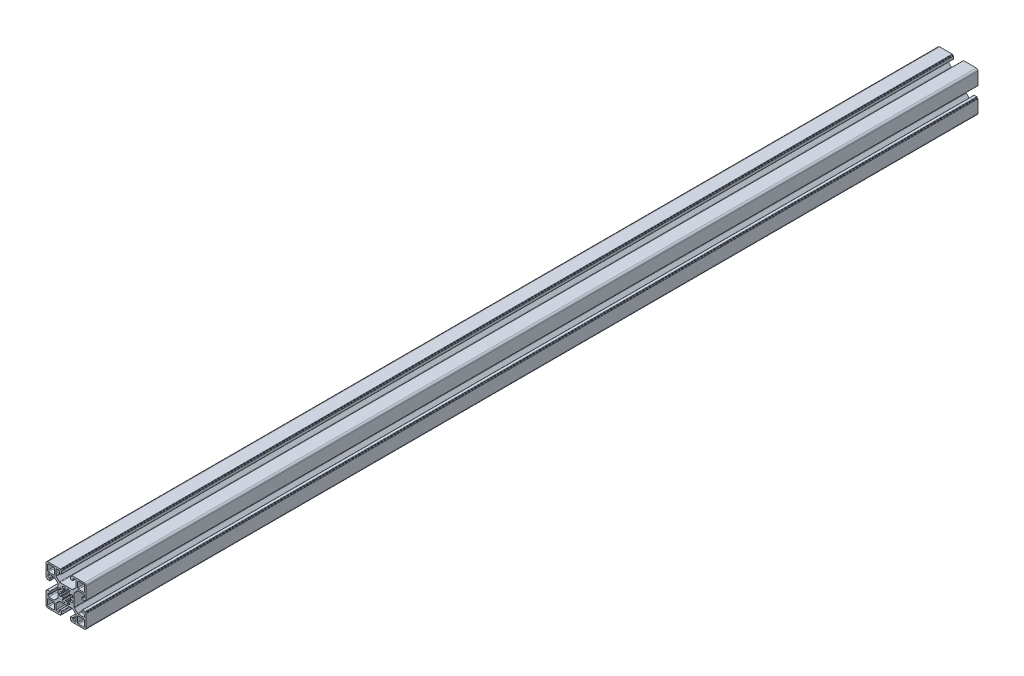
SolidWorks part; units mm, degrees
material "6063 T5"
ref_plane "Спереди" through (0, 0, 0) normal (0, 0, 1) x (1, 0, 0)
ref_plane "Сверху" through (0, 0, 0) normal (0, 1, 0) x (1, 0, 0)
ref_plane "Справа" through (0, 0, 0) normal (1, 0, 0) x (0, 0, -1)
sketch "Эскиз1" plane through (0, 0, 0) normal (0, 0, 1) x (1, 0, 0)
  line L0 (-19.98, 20.5457) -> (20.02, 20.5457) construction
  line L1 (-22.5, 11.25) -> (-22.5, 20.5)
  line L2 (-20.5, 22.5) -> (-11.25, 22.5)
  line L3 (11.25, 22.5) -> (20.5, 22.5)
  line L4 (-14, 13) -> (-19.8, 13)
  line L5 (-13, 14) -> (-13, 19.8)
  line L6 (-14, 20.8) -> (-19.8, 20.8)
  line L7 (-20.8, 14) -> (-20.8, 19.8)
  line L8 (22.5, 20.5) -> (22.5, 11.25)
  line L9 (13, 14) -> (13, 19.8)
  line L10 (14, 13) -> (19.8, 13)
  line L11 (20.8, 14) -> (20.8, 19.8)
  line L12 (14, 20.8) -> (19.8, 20.8)
  line L13 (22.5, -11.25) -> (22.5, -20.5)
  line L14 (20.5, -22.5) -> (11.25, -22.5)
  line L15 (14, -13) -> (19.8, -13)
  line L16 (13, -14) -> (13, -19.8)
  line L17 (14, -20.8) -> (19.8, -20.8)
  line L18 (20.8, -14) -> (20.8, -19.8)
  line L19 (-11.25, -22.5) -> (-20.5, -22.5)
  line L20 (-22.5, -20.5) -> (-22.5, -11.25)
  line L21 (-13, -14) -> (-13, -19.8)
  line L22 (-14, -13) -> (-19.8, -13)
  line L23 (-20.8, -14) -> (-20.8, -19.8)
  line L24 (-14, -20.8) -> (-19.8, -20.8)
  line L25 (0, 0) -> (-13, 14) construction
  line L26 (-22.5383, 27.0237) -> (22.4617, 27.0237) construction
  arc A0 (-22.5, 20.5) -> (-20.5, 22.5) centre (-20.5, 20.5) cw
  arc A1 (-19.8, 20.8) -> (-20.8, 19.8) centre (-19.8, 19.8) ccw
  arc A2 (-19.8, 13) -> (-20.8, 14) centre (-19.8, 14) cw
  arc A3 (-14, 13) -> (-13, 14) centre (-14, 14) ccw
  arc A4 (-13, 19.8) -> (-14, 20.8) centre (-14, 19.8) ccw
  arc A6 (20.5, 22.5) -> (22.5, 20.5) centre (20.5, 20.5) cw
  arc A7 (20.8, 19.8) -> (19.8, 20.8) centre (19.8, 19.8) ccw
  arc A8 (13, 19.8) -> (14, 20.8) centre (14, 19.8) cw
  arc A9 (13, 14) -> (14, 13) centre (14, 14) ccw
  arc A10 (19.8, 13) -> (20.8, 14) centre (19.8, 14) ccw
  arc A11 (22.5, -20.5) -> (20.5, -22.5) centre (20.5, -20.5) cw
  arc A12 (19.8, -20.8) -> (20.8, -19.8) centre (19.8, -19.8) ccw
  arc A13 (19.8, -13) -> (20.8, -14) centre (19.8, -14) cw
  arc A14 (14, -13) -> (13, -14) centre (14, -14) ccw
  arc A15 (13, -19.8) -> (14, -20.8) centre (14, -19.8) ccw
  arc A16 (-20.5, -22.5) -> (-22.5, -20.5) centre (-20.5, -20.5) cw
  arc A17 (-20.8, -19.8) -> (-19.8, -20.8) centre (-19.8, -19.8) ccw
  arc A18 (-13, -19.8) -> (-14, -20.8) centre (-14, -19.8) cw
  arc A19 (-13, -14) -> (-14, -13) centre (-14, -14) ccw
  arc A20 (-19.8, -13) -> (-20.8, -14) centre (-19.8, -14) ccw
  point P5 (0, 0)
  line B0 (-22.5, 11.25) -> (-22.5, 6.4)
  line B1 (-22.2, 6.1) -> (-21.8, 6.1)
  line B2 (-21.5, 5.8) -> (-21.5, 5.4)
  line B3 (-21.2, 5.1) -> (-18.3, 5.1)
  line B4 (-18, 5.4) -> (-18, 7.3)
  line B5 (-18.3, 7.6) -> (-19.5, 7.6)
  line B6 (-20.5, 8.6) -> (-20.5, 10.25)
  line B7 (-19.5, 11.25) -> (-13.5642, 11.25)
  line B8 (-12.8571, 10.9571) -> (-9.4429, 7.5429)
  line B9 (-9.15, 6.8358) -> (-9.15, -6.8358)
  line B10 (-9.15, 0) -> (-22.5, 0) construction
  line B11 (-12.8571, -10.9571) -> (-9.4429, -7.5429)
  line B12 (-19.5, -11.25) -> (-13.5642, -11.25)
  line B13 (-20.5, -8.6) -> (-20.5, -10.25)
  line B14 (-18.3, -7.6) -> (-19.5, -7.6)
  line B15 (-18, -5.4) -> (-18, -7.3)
  line B16 (-21.2, -5.1) -> (-18.3, -5.1)
  line B17 (-21.5, -5.8) -> (-21.5, -5.4)
  line B18 (-22.2, -6.1) -> (-21.8, -6.1)
  line B19 (-22.5, -11.25) -> (-22.5, -6.4)
  arc B20 (-18, 7.3) -> (-18.3, 7.6) centre (-18.3, 7.3) ccw
  arc B21 (-18.3, 5.1) -> (-18, 5.4) centre (-18.3, 5.4) ccw
  arc B22 (-21.5, 5.4) -> (-21.2, 5.1) centre (-21.2, 5.4) ccw
  arc B23 (-21.8, 6.1) -> (-21.5, 5.8) centre (-21.8, 5.8) cw
  arc B24 (-22.5, 6.4) -> (-22.2, 6.1) centre (-22.2, 6.4) ccw
  arc B25 (-9.4429, 7.5429) -> (-9.15, 6.8358) centre (-10.15, 6.8358) cw
  arc B26 (-13.5642, 11.25) -> (-12.8571, 10.9571) centre (-13.5642, 10.25) cw
  arc B27 (-20.5, 10.25) -> (-19.5, 11.25) centre (-19.5, 10.25) cw
  arc B28 (-19.5, 7.6) -> (-20.5, 8.6) centre (-19.5, 8.6) cw
  arc B29 (-19.5, -7.6) -> (-20.5, -8.6) centre (-19.5, -8.6) ccw
  arc B30 (-20.5, -10.25) -> (-19.5, -11.25) centre (-19.5, -10.25) ccw
  arc B31 (-13.5642, -11.25) -> (-12.8571, -10.9571) centre (-13.5642, -10.25) ccw
  arc B32 (-9.4429, -7.5429) -> (-9.15, -6.8358) centre (-10.15, -6.8358) ccw
  arc B33 (-22.5, -6.4) -> (-22.2, -6.1) centre (-22.2, -6.4) cw
  arc B34 (-21.8, -6.1) -> (-21.5, -5.8) centre (-21.8, -5.8) ccw
  arc B35 (-21.5, -5.4) -> (-21.2, -5.1) centre (-21.2, -5.4) cw
  arc B36 (-18.3, -5.1) -> (-18, -5.4) centre (-18.3, -5.4) cw
  arc B37 (-18, -7.3) -> (-18.3, -7.6) centre (-18.3, -7.3) cw
  line B38 (11.25, 22.5) -> (6.4, 22.5)
  line B39 (6.1, 22.2) -> (6.1, 21.8)
  line B40 (5.8, 21.5) -> (5.4, 21.5)
  line B41 (5.1, 21.2) -> (5.1, 18.3)
  line B42 (5.4, 18) -> (7.3, 18)
  line B43 (7.6, 18.3) -> (7.6, 19.5)
  line B44 (8.6, 20.5) -> (10.25, 20.5)
  line B45 (11.25, 19.5) -> (11.25, 13.5642)
  line B46 (10.9571, 12.8571) -> (7.5429, 9.4429)
  line B47 (6.8358, 9.15) -> (-6.8358, 9.15)
  line B48 (0, 9.15) -> (0, 22.5) construction
  line B49 (-10.9571, 12.8571) -> (-7.5429, 9.4429)
  line B50 (-11.25, 19.5) -> (-11.25, 13.5642)
  line B51 (-8.6, 20.5) -> (-10.25, 20.5)
  line B52 (-7.6, 18.3) -> (-7.6, 19.5)
  line B53 (-5.4, 18) -> (-7.3, 18)
  line B54 (-5.1, 21.2) -> (-5.1, 18.3)
  line B55 (-5.8, 21.5) -> (-5.4, 21.5)
  line B56 (-6.1, 22.2) -> (-6.1, 21.8)
  line B57 (-11.25, 22.5) -> (-6.4, 22.5)
  arc B58 (7.3, 18) -> (7.6, 18.3) centre (7.3, 18.3) ccw
  arc B59 (5.1, 18.3) -> (5.4, 18) centre (5.4, 18.3) ccw
  arc B60 (5.4, 21.5) -> (5.1, 21.2) centre (5.4, 21.2) ccw
  arc B61 (6.1, 21.8) -> (5.8, 21.5) centre (5.8, 21.8) cw
  arc B62 (6.4, 22.5) -> (6.1, 22.2) centre (6.4, 22.2) ccw
  arc B63 (7.5429, 9.4429) -> (6.8358, 9.15) centre (6.8358, 10.15) cw
  arc B64 (11.25, 13.5642) -> (10.9571, 12.8571) centre (10.25, 13.5642) cw
  arc B65 (10.25, 20.5) -> (11.25, 19.5) centre (10.25, 19.5) cw
  arc B66 (7.6, 19.5) -> (8.6, 20.5) centre (8.6, 19.5) cw
  arc B67 (-7.6, 19.5) -> (-8.6, 20.5) centre (-8.6, 19.5) ccw
  arc B68 (-10.25, 20.5) -> (-11.25, 19.5) centre (-10.25, 19.5) ccw
  arc B69 (-11.25, 13.5642) -> (-10.9571, 12.8571) centre (-10.25, 13.5642) ccw
  arc B70 (-7.5429, 9.4429) -> (-6.8358, 9.15) centre (-6.8358, 10.15) ccw
  arc B71 (-6.4, 22.5) -> (-6.1, 22.2) centre (-6.4, 22.2) cw
  arc B72 (-6.1, 21.8) -> (-5.8, 21.5) centre (-5.8, 21.8) ccw
  arc B73 (-5.4, 21.5) -> (-5.1, 21.2) centre (-5.4, 21.2) cw
  arc B74 (-5.1, 18.3) -> (-5.4, 18) centre (-5.4, 18.3) cw
  arc B75 (-7.3, 18) -> (-7.6, 18.3) centre (-7.3, 18.3) cw
  line B76 (22.5, -11.25) -> (22.5, -6.4)
  line B77 (22.2, -6.1) -> (21.8, -6.1)
  line B78 (21.5, -5.8) -> (21.5, -5.4)
  line B79 (21.2, -5.1) -> (18.3, -5.1)
  line B80 (18, -5.4) -> (18, -7.3)
  line B81 (18.3, -7.6) -> (19.5, -7.6)
  line B82 (20.5, -8.6) -> (20.5, -10.25)
  line B83 (19.5, -11.25) -> (13.5642, -11.25)
  line B84 (12.8571, -10.9571) -> (9.4429, -7.5429)
  line B85 (9.15, -6.8358) -> (9.15, 6.8358)
  line B86 (9.15, 0) -> (22.5, 0) construction
  line B87 (12.8571, 10.9571) -> (9.4429, 7.5429)
  line B88 (19.5, 11.25) -> (13.5642, 11.25)
  line B89 (20.5, 8.6) -> (20.5, 10.25)
  line B90 (18.3, 7.6) -> (19.5, 7.6)
  line B91 (18, 5.4) -> (18, 7.3)
  line B92 (21.2, 5.1) -> (18.3, 5.1)
  line B93 (21.5, 5.8) -> (21.5, 5.4)
  line B94 (22.2, 6.1) -> (21.8, 6.1)
  line B95 (22.5, 11.25) -> (22.5, 6.4)
  arc B96 (18, -7.3) -> (18.3, -7.6) centre (18.3, -7.3) ccw
  arc B97 (18.3, -5.1) -> (18, -5.4) centre (18.3, -5.4) ccw
  arc B98 (21.5, -5.4) -> (21.2, -5.1) centre (21.2, -5.4) ccw
  arc B99 (21.8, -6.1) -> (21.5, -5.8) centre (21.8, -5.8) cw
  arc B100 (22.5, -6.4) -> (22.2, -6.1) centre (22.2, -6.4) ccw
  arc B101 (9.4429, -7.5429) -> (9.15, -6.8358) centre (10.15, -6.8358) cw
  arc B102 (13.5642, -11.25) -> (12.8571, -10.9571) centre (13.5642, -10.25) cw
  arc B103 (20.5, -10.25) -> (19.5, -11.25) centre (19.5, -10.25) cw
  arc B104 (19.5, -7.6) -> (20.5, -8.6) centre (19.5, -8.6) cw
  arc B105 (19.5, 7.6) -> (20.5, 8.6) centre (19.5, 8.6) ccw
  arc B106 (20.5, 10.25) -> (19.5, 11.25) centre (19.5, 10.25) ccw
  arc B107 (13.5642, 11.25) -> (12.8571, 10.9571) centre (13.5642, 10.25) ccw
  arc B108 (9.4429, 7.5429) -> (9.15, 6.8358) centre (10.15, 6.8358) ccw
  arc B109 (22.5, 6.4) -> (22.2, 6.1) centre (22.2, 6.4) cw
  arc B110 (21.8, 6.1) -> (21.5, 5.8) centre (21.8, 5.8) ccw
  arc B111 (21.5, 5.4) -> (21.2, 5.1) centre (21.2, 5.4) cw
  arc B112 (18.3, 5.1) -> (18, 5.4) centre (18.3, 5.4) cw
  arc B113 (18, 7.3) -> (18.3, 7.6) centre (18.3, 7.3) cw
  line B114 (-11.25, -22.5) -> (-6.4, -22.5)
  line B115 (-6.1, -22.2) -> (-6.1, -21.8)
  line B116 (-5.8, -21.5) -> (-5.4, -21.5)
  line B117 (-5.1, -21.2) -> (-5.1, -18.3)
  line B118 (-5.4, -18) -> (-7.3, -18)
  line B119 (-7.6, -18.3) -> (-7.6, -19.5)
  line B120 (-8.6, -20.5) -> (-10.25, -20.5)
  line B121 (-11.25, -19.5) -> (-11.25, -13.5642)
  line B122 (-10.9571, -12.8571) -> (-7.5429, -9.4429)
  line B123 (-6.8358, -9.15) -> (6.8358, -9.15)
  line B124 (0, -9.15) -> (0, -22.5) construction
  line B125 (10.9571, -12.8571) -> (7.5429, -9.4429)
  line B126 (11.25, -19.5) -> (11.25, -13.5642)
  line B127 (8.6, -20.5) -> (10.25, -20.5)
  line B128 (7.6, -18.3) -> (7.6, -19.5)
  line B129 (5.4, -18) -> (7.3, -18)
  line B130 (5.1, -21.2) -> (5.1, -18.3)
  line B131 (5.8, -21.5) -> (5.4, -21.5)
  line B132 (6.1, -22.2) -> (6.1, -21.8)
  line B133 (11.25, -22.5) -> (6.4, -22.5)
  arc B134 (-7.3, -18) -> (-7.6, -18.3) centre (-7.3, -18.3) ccw
  arc B135 (-5.1, -18.3) -> (-5.4, -18) centre (-5.4, -18.3) ccw
  arc B136 (-5.4, -21.5) -> (-5.1, -21.2) centre (-5.4, -21.2) ccw
  arc B137 (-6.1, -21.8) -> (-5.8, -21.5) centre (-5.8, -21.8) cw
  arc B138 (-6.4, -22.5) -> (-6.1, -22.2) centre (-6.4, -22.2) ccw
  arc B139 (-7.5429, -9.4429) -> (-6.8358, -9.15) centre (-6.8358, -10.15) cw
  arc B140 (-11.25, -13.5642) -> (-10.9571, -12.8571) centre (-10.25, -13.5642) cw
  arc B141 (-10.25, -20.5) -> (-11.25, -19.5) centre (-10.25, -19.5) cw
  arc B142 (-7.6, -19.5) -> (-8.6, -20.5) centre (-8.6, -19.5) cw
  arc B143 (7.6, -19.5) -> (8.6, -20.5) centre (8.6, -19.5) ccw
  arc B144 (10.25, -20.5) -> (11.25, -19.5) centre (10.25, -19.5) ccw
  arc B145 (11.25, -13.5642) -> (10.9571, -12.8571) centre (10.25, -13.5642) ccw
  arc B146 (7.5429, -9.4429) -> (6.8358, -9.15) centre (6.8358, -10.15) ccw
  arc B147 (6.4, -22.5) -> (6.1, -22.2) centre (6.4, -22.2) cw
  arc B148 (6.1, -21.8) -> (5.8, -21.5) centre (5.8, -21.8) ccw
  arc B149 (5.4, -21.5) -> (5.1, -21.2) centre (5.4, -21.2) cw
  arc B150 (5.1, -18.3) -> (5.4, -18) centre (5.4, -18.3) cw
  arc B151 (7.3, -18) -> (7.6, -18.3) centre (7.3, -18.3) cw
  line B152 (0, 0) -> (3.6062, 3.6062) construction
  line B153 (1.3637, 7.358) -> (1.0164, 5.4842)
  line B154 (3.1592, 4.5967) -> (4.2386, 6.1672)
  line B155 (0, 0) -> (0, 5.1) construction
  arc B156 (0.478, -5.0776) -> (-0.478, -5.0776) centre (0, 0) cw
  arc B157 (-6.8804, -4.0816) -> (-7.7513, -1.979) centre (0, 0) cw
  arc B158 (3.9283, 3.2524) -> (3.2524, 3.9283) centre (0, 0) ccw
  arc B159 (4.0816, 6.8804) -> (1.979, 7.7513) centre (0, 0) ccw
  arc B160 (0.478, 5.0776) -> (-0.478, 5.0776) centre (0, 0) ccw
  line B161 (-1.3637, 7.358) -> (-1.0164, 5.4842)
  arc B162 (4.0816, -6.8804) -> (1.979, -7.7513) centre (0, 0) cw
  arc B163 (-3.9283, -3.2524) -> (-3.2524, -3.9283) centre (0, 0) ccw
  line B164 (-3.1592, -4.5967) -> (-4.2386, -6.1672)
  line B165 (0, 0) -> (6.3318, 0) construction
  line B166 (4.5967, 3.1592) -> (6.1672, 4.2386)
  line B167 (7.358, 1.3637) -> (5.4842, 1.0164)
  line B168 (-7.358, 1.3637) -> (-5.4842, 1.0164)
  line B169 (-4.5967, 3.1592) -> (-6.1672, 4.2386)
  line B170 (-3.1592, 4.5967) -> (-4.2386, 6.1672)
  line B171 (7.358, -1.3637) -> (5.4842, -1.0164)
  line B172 (4.5967, -3.1592) -> (6.1672, -4.2386)
  line B173 (3.1592, -4.5967) -> (4.2386, -6.1672)
  line B174 (1.3637, -7.358) -> (1.0164, -5.4842)
  line B175 (-1.3637, -7.358) -> (-1.0164, -5.4842)
  line B176 (-4.5967, -3.1592) -> (-6.1672, -4.2386)
  line B177 (-7.358, -1.3637) -> (-5.4842, -1.0164)
  arc B178 (5.0776, 0.478) -> (5.0776, -0.478) centre (0, 0) cw
  arc B179 (6.8804, 4.0816) -> (7.7513, 1.979) centre (0, 0) cw
  arc B180 (-5.0776, 0.478) -> (-5.0776, -0.478) centre (0, 0) ccw
  arc B181 (-6.8804, 4.0816) -> (-7.7513, 1.979) centre (0, 0) ccw
  arc B182 (-3.9283, 3.2524) -> (-3.2524, 3.9283) centre (0, 0) cw
  arc B183 (-4.0816, 6.8804) -> (-1.979, 7.7513) centre (0, 0) cw
  arc B184 (6.8804, -4.0816) -> (7.7513, -1.979) centre (0, 0) ccw
  arc B185 (3.9283, -3.2524) -> (3.2524, -3.9283) centre (0, 0) cw
  arc B186 (-4.0816, -6.8804) -> (-1.979, -7.7513) centre (0, 0) ccw
  arc B187 (5.0776, 0.478) -> (5.4842, 1.0164) centre (5.5754, 0.5248) cw
  arc B188 (5.4842, -1.0164) -> (5.0776, -0.478) centre (5.5754, -0.5248) cw
  arc B189 (7.7513, -1.979) -> (7.358, -1.3637) centre (7.2669, -1.8554) ccw
  arc B190 (6.8804, -4.0816) -> (6.1672, -4.2386) centre (6.4504, -3.8265) cw
  arc B191 (3.9283, -3.2524) -> (4.5967, -3.1592) centre (4.3135, -3.5713) cw
  arc B192 (3.2524, -3.9283) -> (3.1592, -4.5967) centre (3.5713, -4.3135) ccw
  arc B193 (4.0816, -6.8804) -> (4.2386, -6.1672) centre (3.8265, -6.4504) ccw
  arc B194 (1.979, -7.7513) -> (1.3637, -7.358) centre (1.8554, -7.2669) cw
  arc B195 (0.478, -5.0776) -> (1.0164, -5.4842) centre (0.5248, -5.5754) cw
  arc B196 (-0.478, -5.0776) -> (-1.0164, -5.4842) centre (-0.5248, -5.5754) ccw
  arc B197 (-1.979, -7.7513) -> (-1.3637, -7.358) centre (-1.8554, -7.2669) ccw
  arc B198 (-4.0816, -6.8804) -> (-4.2386, -6.1672) centre (-3.8265, -6.4504) cw
  arc B199 (-3.2524, -3.9283) -> (-3.1592, -4.5967) centre (-3.5713, -4.3135) cw
  arc B200 (-3.9283, -3.2524) -> (-4.5967, -3.1592) centre (-4.3135, -3.5713) ccw
  arc B201 (-6.8804, -4.0816) -> (-6.1672, -4.2386) centre (-6.4504, -3.8265) ccw
  arc B202 (-7.7513, -1.979) -> (-7.358, -1.3637) centre (-7.2669, -1.8554) cw
  arc B203 (-5.4842, -1.0164) -> (-5.0776, -0.478) centre (-5.5754, -0.5248) ccw
  arc B204 (-5.0776, 0.478) -> (-5.4842, 1.0164) centre (-5.5754, 0.5248) ccw
  arc B205 (-7.7513, 1.979) -> (-7.358, 1.3637) centre (-7.2669, 1.8554) ccw
  arc B206 (-6.8804, 4.0816) -> (-6.1672, 4.2386) centre (-6.4504, 3.8265) cw
  arc B207 (-3.9283, 3.2524) -> (-4.5967, 3.1592) centre (-4.3135, 3.5713) cw
  arc B208 (-3.2524, 3.9283) -> (-3.1592, 4.5967) centre (-3.5713, 4.3135) ccw
  arc B209 (-4.0816, 6.8804) -> (-4.2386, 6.1672) centre (-3.8265, 6.4504) ccw
  arc B210 (-1.979, 7.7513) -> (-1.3637, 7.358) centre (-1.8554, 7.2669) cw
  arc B211 (-1.0164, 5.4842) -> (-0.478, 5.0776) centre (-0.5248, 5.5754) ccw
  arc B212 (1.0164, 5.4842) -> (0.478, 5.0776) centre (0.5248, 5.5754) cw
  arc B213 (1.3637, 7.358) -> (1.979, 7.7513) centre (1.8554, 7.2669) cw
  arc B214 (4.2386, 6.1672) -> (4.0816, 6.8804) centre (3.8265, 6.4504) ccw
  arc B215 (3.1592, 4.5967) -> (3.2524, 3.9283) centre (3.5713, 4.3135) ccw
  arc B216 (4.5967, 3.1592) -> (3.9283, 3.2524) centre (4.3135, 3.5713) cw
  arc B217 (6.1672, 4.2386) -> (6.8804, 4.0816) centre (6.4504, 3.8265) cw
  arc B218 (7.7513, 1.979) -> (7.358, 1.3637) centre (7.2669, 1.8554) cw
  dimension "D2" = 2
  dimension "D5" = 1
  dimension "D6" = 4
  dimension "D1" = 22.5
  dimension "D4" = 7.8
  dimension "D7" = 45
  dimension "D8" = 1.7
  dimension "D9" = 1.7
sketch_block_instance "8B(20,5PL)-1"
sketch_block "8B(20,5PL)" parameters "D7"=0.3, "D8"=1, "D1"=13.35, "D2"=4.5, "D3"=10.2, "D4"=22.5, "D5"=12.2, "D6"=135, "D9"=11.8, "D10"=4.85, "D11"=1.4, "D12"=1.65
sketch_block_instance "8B(20,5PL)-3"
sketch_block_instance "8B(20,5PL)-4"
sketch_block_instance "8B(20,5PL)-5"
sketch_block_instance "star_R5,1_R8-1"
sketch_block "star_R5,1_R8" parameters "D1"=10.2, "D5"=16, "D6"=0.5, "D2"=10.5, "D3"=24, "D4"=45
extrude "Бобышка-Вытянуть1" add sketch "Эскиз1" along normal blind 1000 contours B151 B129 B150 B130 B149 B131 B148 B132 B147 B133 L14 A11 L13 B76 B100 B77 B99 B78 B98 B79 B97 B80 B96 B81 B104 B82 B103 B83 B102 B84 B101 B85 B108 B87 B107 B88 B106 B89 B105 B90 B113 B91 B112 B92 B111 B93 B110 B94 B109 B95 L8
